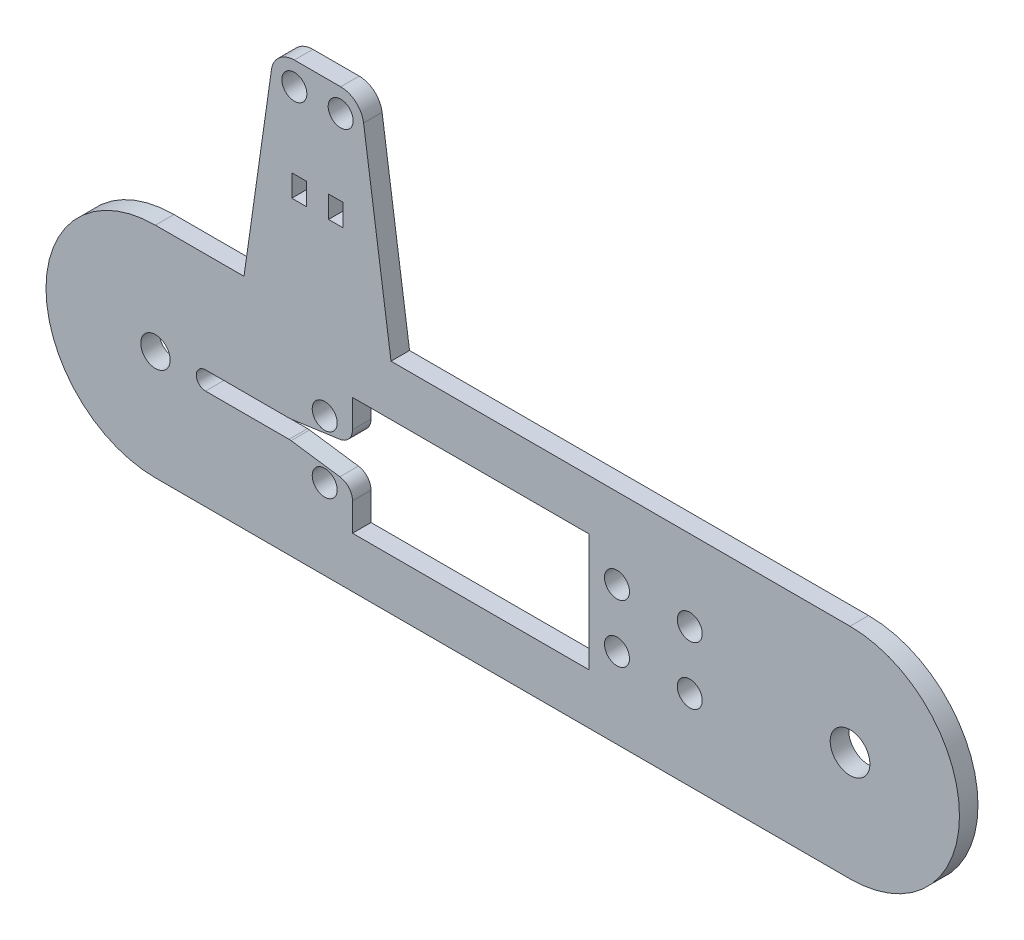
SolidWorks part; units mm, degrees
ref_plane "Front Plane" through (0, 0, 0) normal (0, 0, 1) x (1, 0, 0)
ref_plane "Top Plane" through (0, 0, 0) normal (0, 1, 0) x (1, 0, 0)
ref_plane "Right Plane" through (0, 0, 0) normal (1, 0, 0) x (0, 0, -1)
sketch "Sketch1" plane through (0, 0, 0) normal (0, 0, 1) x (1, 0, 0)
  line L8 (0, 18.9078) -> (120.015, 18.9078) construction
  line L18 (120.015, 37.8155) -> (0, 37.8155)
  line L37 (0, 0) -> (120.015, 0)
  line L42 (120.015, 37.8155) -> (120.015, 0) construction
  line L43 (0, 37.8155) -> (0, 0) construction
  line L55 (60.0075, 37.8155) -> (60.0075, 18.9078) construction
  circle A21 centre (120.015, 18.9078) radius 3.429
  circle A22 centre (0, 18.9078) radius 2.54
  arc A25 (120.015, 37.8155) -> (120.015, 0) centre (120.015, 18.9078) cw
  arc A26 (0, 0) -> (0, 37.8155) centre (0, 18.9078) cw
  dimension "D5" = 18.9078
  dimension "D2" = 5.08
  dimension "D1" = 6.858
  dimension "D7" = 120.015
extrude "Boss-Extrude1" add sketch "Sketch1" along normal blind 3.2004
sketch "Sketch5" plane through (0, 0, 0) normal (0, 0, -1) x (-1, 0, 0)
  line L0 (0, 18.9078) -> (-120.015, 18.9078) construction
  line L5 (-92.3222, 13.9078) -> (-92.3222, 23.9078) construction
  line L6 (-74.944, 29.0678) -> (-74.944, 8.7478)
  line L7 (-34.05, 29.0678) -> (-34.05, 8.7478)
  line L12 (-54.497, 29.0678) -> (-54.497, 8.7478) construction
  line L13 (-79.747, 13.9078) -> (-79.747, 23.9078) construction
  line L14 (-29.247, 13.9078) -> (-29.247, 23.9078) construction
  line L15 (-79.747, 18.9078) -> (-29.247, 18.9078) construction
  line L19 (-92.3222, 18.9078) -> (-79.747, 18.9078) construction
  line L21 (-74.944, 8.7478) -> (-34.05, 8.7478)
  line L25 (-74.944, 29.0678) -> (-34.05, 29.0678)
  circle A0 centre (-79.747, 23.9078) radius 2.159
  circle A1 centre (-29.247, 13.9078) radius 2.159
  circle A2 centre (-29.247, 23.9078) radius 2.159
  circle A3 centre (-79.747, 13.9078) radius 2.159
  circle A5 centre (0, 18.9078) radius 2.54 construction
  circle A8 centre (-92.3222, 23.9078) radius 2.159
  circle A9 centre (-92.3222, 13.9078) radius 2.159
  point P6 (-44.45, 18.9078)
  point P9 (-54.497, 18.9078)
  dimension "D2" = 4.318
  dimension "D3" = 40.894
  dimension "D1" = 50.5
  dimension "D4" = 20.32
  dimension "D5" = 10.4
  dimension "D6" = 44.45
  dimension "D7" = 10
  dimension "D8" = 12.5752
extrude "Cut-Extrude3" cut sketch "Sketch5" against normal through all
sketch "Sketch6" plane through (0, 0, 3.2004) normal (0, 0, 1) x (1, 0, 0)
  line L0 (16.905, 18.9078) -> (34.05, 18.9078) construction
  line L1 (8.65, 20.4953) -> (25.16, 20.4953)
  line L2 (8.65, 20.4953) -> (8.65, 17.3203) construction
  line L3 (8.65, 17.3203) -> (25.16, 17.3203)
  line L4 (25.16, 20.4953) -> (25.16, 17.3203) construction
  line L5 (34.05, 8.7478) -> (34.05, 29.0678) construction
  line L6 (16.905, 20.4953) -> (16.905, 17.3203) construction
  arc A0 (8.65, 20.4953) -> (8.65, 17.3203) centre (8.65, 18.9078) ccw
  arc A1 (25.16, 20.4953) -> (25.16, 17.3203) centre (25.16, 18.9078) cw
  dimension "D1" = 25.4
  dimension "D2" = 3.175
  dimension "D3" = 16.51
extrude "Cut-Extrude4" cut sketch "Sketch6" against normal up to surface (3.2004 mm away) up to face at (90.1632, 23.9078, 0)
sketch "Sketch8" plane through (0, 0, 3.2004) normal (0, 0, 1) x (1, 0, 0)
  line L0 (28.208, 21.1938) -> (28.208, 16.6218) construction
  line L1 (34.05, 15.7963) -> (34.05, 22.0193)
  line L2 (34.05, 15.7963) -> (23.2648, 17.3203)
  line L4 (34.05, 22.0193) -> (23.2648, 20.4953)
  line L5 (34.05, 18.9078) -> (28.208, 18.9078) construction
  line L6 (34.05, 8.7478) -> (34.05, 29.0678) construction
  line L8 (25.16, 20.4953) -> (8.65, 20.4953) construction
  line L9 (8.65, 17.3203) -> (25.16, 17.3203) construction
  line L10 (23.2648, 20.4953) -> (23.2648, 17.3203)
  point P1 (0, 0)
  point P4 (34.05, 18.9078)
  point P11 (0, 0)
  dimension "D1" = 6.223
  dimension "D2" = 4.572
  dimension "D3" = 5.842
extrude "Cut-Extrude5" cut sketch "Sketch8" against normal up to surface (3.2004 mm away) up to face at (16.905, 18.9078, 0)
sketch "Sketch9" plane through (0, 0, 0) normal (0, 0, -1) x (-1, 0, 0)
  line L0 (-120.015, 37.8155) -> (0, 37.8155) construction
  line L3 (-40.7035, 37.8155) -> (-15.3035, 37.8155)
  line L5 (-28.0035, 74.5312) -> (-28.0035, 37.8155) construction
  line L6 (-31.1785, 55.5335) -> (-24.8285, 55.5335) construction
  line L7 (-28.0035, 37.8155) -> (-28.0035, 18.9078) construction
  line L8 (-31.1785, 53.6285) -> (-31.1785, 57.4385) construction
  line L9 (-32.4485, 53.6285) -> (-32.4485, 57.4385)
  line L10 (-32.4485, 53.6285) -> (-29.9085, 53.6285)
  line L11 (-29.9085, 53.6285) -> (-29.9085, 57.4385)
  line L12 (-32.4485, 57.4385) -> (-29.9085, 57.4385)
  line L13 (-24.8285, 53.6285) -> (-24.8285, 57.4385) construction
  line L14 (-26.0985, 53.6285) -> (-26.0985, 57.4385)
  line L15 (-26.0985, 53.6285) -> (-23.5585, 53.6285)
  line L16 (-23.5585, 53.6285) -> (-23.5585, 57.4385)
  line L17 (-26.0985, 57.4385) -> (-23.5585, 57.4385)
  line L18 (-32.004, 74.5312) -> (-24.003, 74.5312)
  line L25 (-32.004, 70.5307) -> (-24.003, 70.5307) construction
  line L26 (-28.208, 18.9078) -> (-28.0035, 18.9078) construction
  line L28 (-35.9645, 71.0947) -> (-40.7035, 37.8155)
  line L29 (-20.0425, 71.0947) -> (-15.3035, 37.8155)
  line L30 (-28.208, 21.1938) -> (-28.208, 16.6218) construction
  circle A0 centre (-32.004, 70.5307) radius 2.159
  circle A1 centre (-24.003, 70.5307) radius 2.159
  arc A3 (-32.004, 74.5312) -> (-35.9645, 71.0947) centre (-32.004, 70.5307) ccw
  arc A6 (-24.003, 74.5312) -> (-20.0425, 71.0947) centre (-24.003, 70.5307) cw
  point P1 (0, 0)
  point P3 (-28.0035, 70.5307)
  point P8 (-28.0035, 55.5335)
  point P12 (-28.0035, 55.5335)
  point P27 (0, 0)
  point P30 (0, 0)
  point P32 (0, 0)
  point P37 (0, 0)
  point P42 (0, 0)
  point P43 (0, 0)
  point P46 (0, 0)
  point P47 (0, 0)
  point P50 (0, 0)
  dimension "D9" = 4.318
  dimension "D1" = 25.4
  dimension "D2" = 4.0005
  dimension "D4" = 3.81
  dimension "D5" = 2.54
  dimension "D6" = 6.35
  dimension "D10" = 0.2045
  dimension "D11" = 8.001
  dimension "D12" = 32.7152
extrude "Boss-Extrude2" add sketch "Sketch9" against normal up to surface (3.2004 mm away) up to face at (90.1632, 23.9078, 3.2004)
fillet "Fillet1" radius 2.54 4 edges at (23.2648, 20.4953, 1.6002) (34.05, 22.0193, 1.6002) (34.05, 15.7963, 1.6002) (23.2648, 17.3203, 1.6002)
